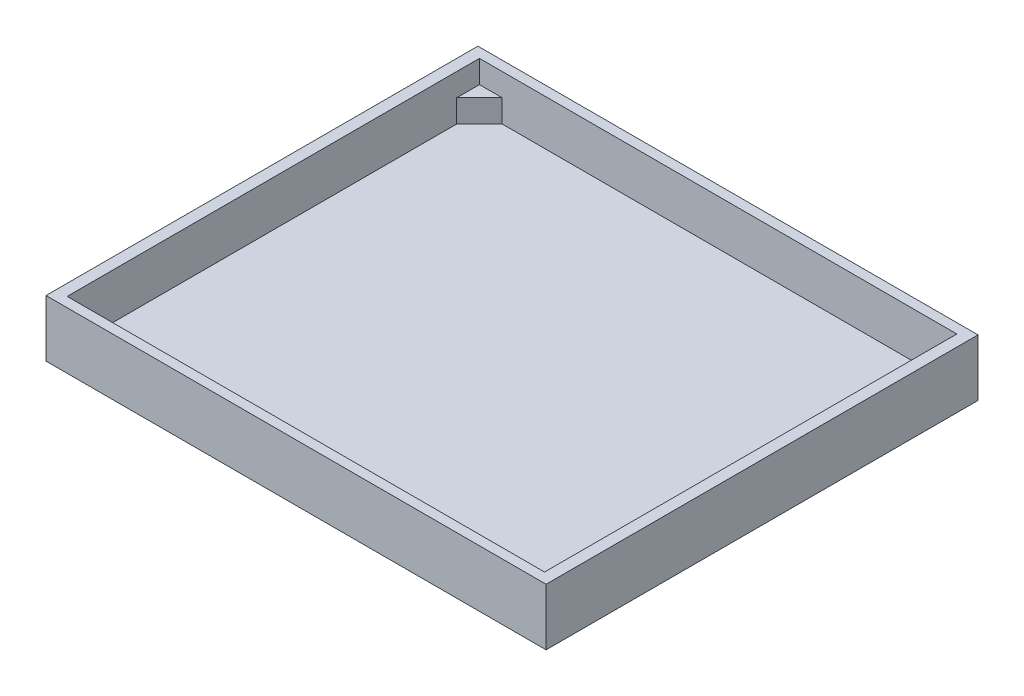
SolidWorks part; units mm, degrees
material "PBT Общее назначение"
ref_plane "Спереди" through (0, 0, 0) normal (0, 0, 1) x (1, 0, 0)
ref_plane "Сверху" through (0, 0, 0) normal (0, 1, 0) x (1, 0, 0)
ref_plane "Справа" through (0, 0, 0) normal (1, 0, 0) x (0, 0, -1)
sketch "Эскиз1" plane through (0, 0, 0) normal (0, 1, 0) x (1, 0, 0)
  line L1 (-5.5, -4.75) -> (5.5, -4.75)
  line L2 (-5.5, -4.75) -> (-5.5, 4.75)
  line L3 (-5.5, 4.75) -> (5.5, 4.75)
  line L4 (5.5, -4.75) -> (5.5, 4.75)
  line L5 (-5.5, -4.75) -> (5.5, 4.75) construction
  line L6 (-5.5, 4.75) -> (5.5, -4.75) construction
  point P0 (0, 0)
  dimension "D1" = 11
  dimension "D2" = 9.5
extrude "Бобышка-Вытянуть1" add sketch "Эскиз1" along normal blind 0.25
sketch "Эскиз2" plane through (0, 0.25, 0) normal (0, 1, 0) x (1, 0, 0)
  line L1 (-5.5, -4.75) -> (5.5, -4.75)
  line L2 (-5.5, -4.75) -> (-5.5, 4.75)
  line L3 (-5.5, 4.75) -> (5.5, 4.75)
  line L4 (5.5, -4.75) -> (5.5, 4.75)
  line L5 (-5.5, -4.75) -> (5.5, 4.75) construction
  line L6 (-5.5, 4.75) -> (5.5, -4.75) construction
  line L7 (-5.25, -4.5341) -> (5.25, -4.5341)
  line L8 (-5.25, -4.5341) -> (-5.25, 4.5341)
  line L9 (-5.25, 4.5341) -> (5.25, 4.5341)
  line L10 (5.25, -4.5341) -> (5.25, 4.5341)
  line L11 (-5.25, -4.5341) -> (5.25, 4.5341) construction
  line L12 (-5.25, 4.5341) -> (5.25, -4.5341) construction
  point P0 (0, 0)
  point P7 (0, 0)
  dimension "D1" = 0.25
extrude "Бобышка-Вытянуть2" add sketch "Эскиз2" along normal blind 1
sketch "Эскиз3" plane through (0, 0.25, 0) normal (0, 1, 0) x (1, 0, 0)
  line L0 (-5.25, 4.5341) -> (-4.75, 4.5341)
  line L1 (5.25, 4.5341) -> (-5.25, 4.5341) construction
  line L2 (-5.25, 4.5341) -> (-5.25, 4.0341)
  line L3 (-5.25, 4.5341) -> (-5.25, -4.5341) construction
  line L4 (0, 0) -> (-0.8078, 0) construction
  line L5 (0, 0) -> (0, 0.9211) construction
  line L6 (-4.75, 4.5341) -> (-5.25, 4.0341)
  line L7 (-5.25, -4.5341) -> (-5.25, -4.0341)
  line L8 (-5.25, -4.5341) -> (-4.75, -4.5341)
  line L9 (-4.75, -4.5341) -> (-5.25, -4.0341)
  line L10 (5.25, -4.5341) -> (5.25, -4.0341)
  line L11 (5.25, -4.5341) -> (4.75, -4.5341)
  line L12 (4.75, -4.5341) -> (5.25, -4.0341)
  line L13 (4.75, 4.5341) -> (5.25, 4.0341)
  line L14 (5.25, 4.5341) -> (4.75, 4.5341)
  line L15 (5.25, 4.5341) -> (5.25, 4.0341)
  dimension "D1" = 0.5
  dimension "D2" = 0.5
extrude "Бобышка-Вытянуть3" add sketch "Эскиз3" along normal blind 0.5
